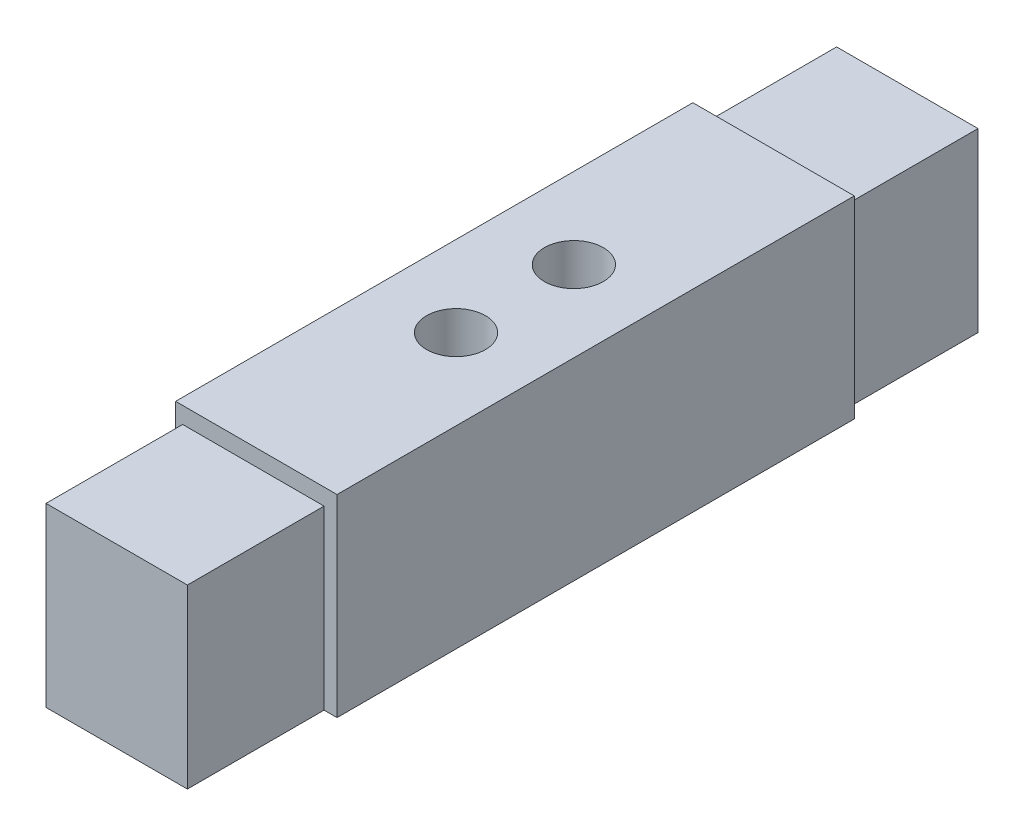
SolidWorks part; units mm, degrees
ref_plane "Front Plane" through (0, 0, 0) normal (0, 0, 1) x (1, 0, 0)
ref_plane "Top Plane" through (0, 0, 0) normal (0, 1, 0) x (1, 0, 0)
ref_plane "Right Plane" through (0, 0, 0) normal (1, 0, 0) x (0, 0, -1)
sketch "Sketch1" plane through (0, 0, 0) normal (0, 0, 1) x (1, 0, 0)
  line L1 (0, 0) -> (34.798, 0)
  line L2 (0, 0) -> (0, 41.656)
  line L3 (0, 41.656) -> (34.798, 41.656)
  line L4 (34.798, 0) -> (34.798, 41.656)
  dimension "D1" = 41.656
  dimension "D2" = 34.798
extrude "Boss-Extrude2" add sketch "Sketch1" along normal blind 111.506 contours L3 L4 L1 L2
sketch "Sketch2" plane through (0, 0, 111.506) normal (0, 0, 1) x (1, 0, 0)
  line L1 (1.524, 0) -> (32.004, 0)
  line L2 (1.524, 0) -> (1.524, 38.1)
  line L3 (1.524, 38.1) -> (32.004, 38.1)
  line L4 (0, 41.656) -> (0, 0)
  line L5 (0, 0) -> (34.798, 0)
  line L6 (34.798, 0) -> (34.798, 41.656)
  line L7 (34.798, 41.656) -> (0, 41.656)
  line L8 (0, 41.656) -> (0, 0)
  line L9 (0, 0) -> (34.798, 0)
  line L10 (34.798, 0) -> (34.798, 41.656)
  line L11 (34.798, 41.656) -> (0, 41.656)
  line L12 (32.004, 0) -> (32.004, 38.1)
  dimension "D2" = 3.556
  dimension "D3" = 1.524
  dimension "D4" = 2.794
  dimension "D1" = 0
extrude "Boss-Extrude3" add sketch "Sketch2" along normal blind 29.464 contours L2 L3 L12 L1
ref_plane "Plane1" through (0, 0, 55.753) normal (0, 0, -1) x (-1, 0, 0)
mirror "Mirror1" about plane through (0, 0, 55.753) normal (0, 0, -1) of "Boss-Extrude3"
sketch "Sketch3" plane through (0, 0, 0) normal (0, -1, 0) x (1, 0, 0)
  line L0 (-19.1389, 55.753) -> (19.1389, 55.753) construction
  line L1 (16.764, -29.464) -> (16.764, 140.97) construction
  line L2 (0, 55.753) -> (34.798, 55.753) construction
  line L13 (0, 0) -> (1.524, 0)
  line L14 (1.524, 0) -> (1.524, -29.464)
  line L15 (1.524, -29.464) -> (32.004, -29.464)
  line L16 (32.004, -29.464) -> (32.004, 0)
  line L17 (32.004, 0) -> (34.798, 0)
  line L18 (34.798, 0) -> (34.798, 111.506)
  line L19 (34.798, 111.506) -> (32.004, 111.506)
  line L20 (32.004, 111.506) -> (32.004, 140.97)
  line L21 (32.004, 140.97) -> (1.524, 140.97)
  line L22 (1.524, 140.97) -> (1.524, 111.506)
  line L23 (1.524, 111.506) -> (0, 111.506)
  line L24 (0, 111.506) -> (0, 0)
  line L25 (0, 0) -> (1.524, 0)
  line L26 (1.524, 0) -> (1.524, -29.464)
  line L27 (1.524, -29.464) -> (32.004, -29.464)
  line L28 (32.004, -29.464) -> (32.004, 0)
  line L29 (32.004, 0) -> (34.798, 0)
  line L30 (34.798, 0) -> (34.798, 111.506)
  line L31 (34.798, 111.506) -> (32.004, 111.506)
  line L32 (32.004, 111.506) -> (32.004, 140.97)
  line L33 (32.004, 140.97) -> (1.524, 140.97)
  line L34 (1.524, 140.97) -> (1.524, 111.506)
  line L35 (1.524, 111.506) -> (0, 111.506)
  line L36 (0, 111.506) -> (0, 0)
  circle A0 centre (16.764, 55.753) radius 6.35
  dimension "D1" = 12.7
  dimension "D2" = 0
extrude "Cut-Extrude2" cut sketch "Sketch3" against normal blind 12.7 contours A0
sketch "Sketch4" plane through (0, 41.656, 0) normal (0, 1, 0) x (1, 0, 0)
  line L0 (17.399, 0) -> (17.399, -112.2884) construction
  line L1 (34.798, -55.753) -> (0, -55.753) construction
  line L4 (34.798, 0) -> (0, 0)
  line L5 (0, 0) -> (0, -111.506)
  line L6 (0, -111.506) -> (34.798, -111.506)
  line L7 (34.798, -111.506) -> (34.798, 0)
  line L8 (34.798, 0) -> (0, 0)
  line L9 (0, 0) -> (0, -111.506)
  line L10 (0, -111.506) -> (34.798, -111.506)
  line L11 (34.798, -111.506) -> (34.798, 0)
  circle A0 centre (17.399, -43.053) radius 6.35
  circle A1 centre (17.399, -68.453) radius 6.35
  dimension "D2" = 12.7
  dimension "D3" = 12.7
  dimension "D4" = 12.7
  dimension "D5" = 12.7
  dimension "D1" = 0
extrude "Cut-Extrude3" cut sketch "Sketch4" against normal blind 12.7 contours A1 | A0
